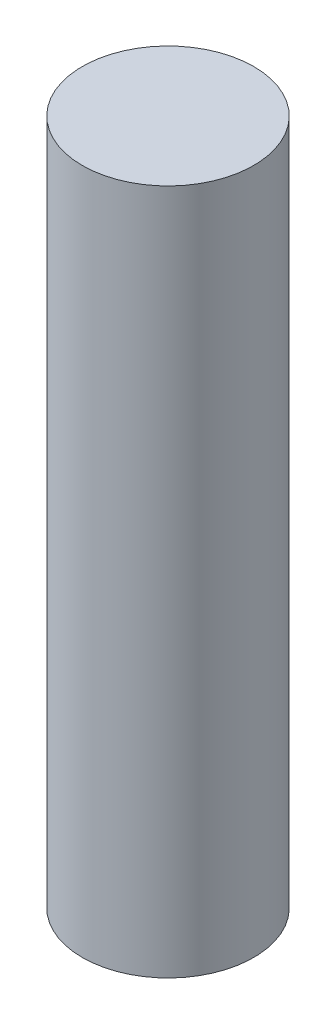
SolidWorks part; units mm, degrees
ref_plane "Front Plane" through (0, 0, 0) normal (0, 0, 1) x (1, 0, 0)
ref_plane "Top Plane" through (0, 0, 0) normal (0, 1, 0) x (1, 0, 0)
ref_plane "Right Plane" through (0, 0, 0) normal (1, 0, 0) x (0, 0, -1)
sketch "Sketch1" plane through (0, 0, 0) normal (0, 1, 0) x (1, 0, 0)
  circle A0 centre (0, 0) radius 10
extrude "Boss-Extrude1" add sketch "Sketch1" along normal blind 80 contours A0
